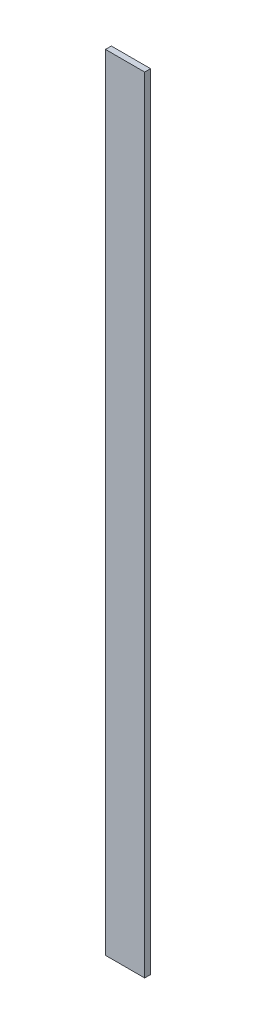
SolidWorks part; units mm, degrees
material "Balsa"
ref_plane "Alzado" through (0, 0, 0) normal (0, 0, 1) x (1, 0, 0)
ref_plane "Planta" through (0, 0, 0) normal (0, 1, 0) x (1, 0, 0)
ref_plane "Vista lateral" through (0, 0, 0) normal (1, 0, 0) x (0, 0, -1)
sketch "Croquis1" plane through (0, 0, 0) normal (0, 0, 1) x (1, 0, 0)
  line L1 (0, 0) -> (20, 0)
  line L2 (0, 0) -> (0, 400)
  line L3 (0, 400) -> (20, 400)
  line L4 (20, 0) -> (20, 400)
  dimension "D1" = 20
  dimension "D2" = 400
extrude "Saliente-Extruir1" add sketch "Croquis1" along normal blind 3
